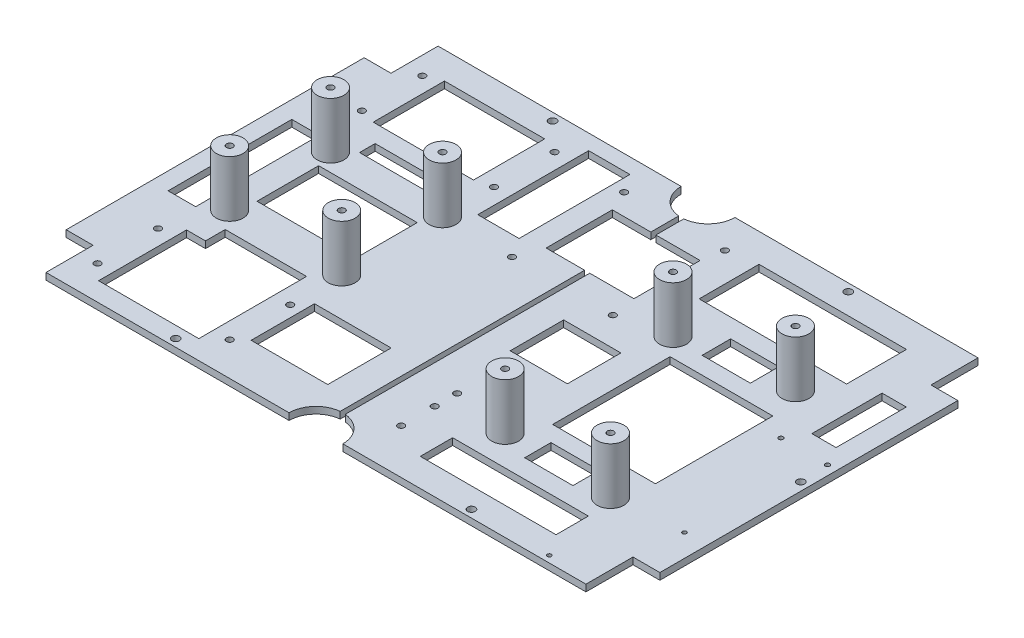
SolidWorks part; units mm, degrees
ref_plane "Płaszczyzna przednia" through (0, 0, 0) normal (0, 0, 1) x (1, 0, 0)
ref_plane "Płaszczyzna górna" through (0, 0, 0) normal (0, 1, 0) x (1, 0, 0)
ref_plane "Płaszczyzna prawa" through (0, 0, 0) normal (1, 0, 0) x (0, 0, -1)
sketch "Sketch1" plane through (0, 0, 0) normal (0, 1, 0) x (1, 0, 0)
  line L16 (-132.5, 87.5) -> (132.5, 87.5)
  line L18 (-132.5, 87.5) -> (-132.5, -87.5)
  line L19 (-132.5, -87.5) -> (132.5, -87.5)
  line L20 (132.5, 87.5) -> (132.5, -87.5)
  line L21 (-132.5, 87.5) -> (132.5, -87.5) construction
  line L22 (-132.5, -87.5) -> (132.5, 87.5) construction
  point P0 (0, 0)
  dimension "D2" = 175
  dimension "D1" = 265
extrude "Boss-Extrude3" add sketch "Sketch1" along normal blind 3
sketch "Sketch2" plane through (0, 3, 0) normal (0, 1, 0) x (1, 0, 0)
  line L2 (-53.5, -45.5) -> (-53.5, 45.5) construction
  line L10 (-132.5, -87.5) -> (-112.5, -87.5) construction
  line L11 (-132.5, -87.5) -> (-132.5, -72.5) construction
  line L12 (-132.5, -72.5) -> (-112.5, -72.5) construction
  line L13 (-112.5, -87.5) -> (-112.5, -72.5) construction
  line L14 (-112.5, -72.5) -> (-53.5, -72.5) construction
  line L15 (-112.5, -72.5) -> (-112.5, -45.5) construction
  line L16 (-112.5, -45.5) -> (-53.5, -45.5) construction
  line L17 (-53.5, -72.5) -> (-53.5, -45.5) construction
  line L18 (-53.5, 45.5) -> (-112.5, 45.5) construction
  line L19 (-53.5, 45.5) -> (-53.5, 72.5) construction
  line L20 (-53.5, 72.5) -> (-112.5, 72.5) construction
  line L21 (-112.5, 45.5) -> (-112.5, 72.5) construction
  line L22 (-53.5, -22.5) -> (-103.5, -22.5) construction
  line L23 (0, 87.5) -> (0, 72.5) construction
  line L28 (132.5, 87.5) -> (-132.5, 87.5) construction
  line L29 (0, 72.5) -> (22.5, 72.5) construction
  line L30 (22.5, 72.5) -> (22.5, 22.5) construction
  line L31 (22.5, 22.5) -> (-22.5, 22.5) construction
  line L32 (-22.5, 22.5) -> (-22.5, 72.5) construction
  line L33 (-22.5, 72.5) -> (0, 72.5) construction
  line L34 (0, -87.5) -> (0, -67.5) construction
  line L35 (-132.5, -87.5) -> (132.5, -87.5) construction
  line L36 (0, -67.5) -> (18, -67.5) construction
  line L37 (18, -67.5) -> (18, -52.5) construction
  line L38 (18, -52.5) -> (18, -42.5) construction
  line L39 (18, -42.5) -> (18, -27.5) construction
  line L40 (-53.5, -22.5) -> (-53.5, 22.5) construction
  line L45 (-53.5, 22.5) -> (-103.5, 22.5) construction
  line L46 (-103.5, -22.5) -> (-103.5, 22.5) construction
  circle A4 centre (18, -67.5) radius 1.45
  circle A5 centre (18, -52.5) radius 1.45
  circle A6 centre (18, -42.5) radius 1.45
  circle A7 centre (18, -27.5) radius 1.45
  circle A8 centre (-53.5, -72.5) radius 1.45
  circle A9 centre (-53.5, -45.5) radius 1.45
  circle A10 centre (-112.5, -45.5) radius 1.45
  circle A11 centre (-112.5, -72.5) radius 1.45
  circle A12 centre (-112.5, 45.5) radius 1.45
  circle A13 centre (-53.5, 45.5) radius 1.45
  circle A14 centre (-53.5, 72.5) radius 1.45
  circle A15 centre (-112.5, 72.5) radius 1.45
  circle A20 centre (-22.5, 22.5) radius 1.45
  circle A21 centre (22.5, 22.5) radius 1.45
  circle A22 centre (-22.5, 72.5) radius 1.45
  circle A23 centre (22.5, 72.5) radius 1.45
  dimension "D3" = 20
  dimension "D11" = 45
  dimension "D4" = 15
  dimension "D5" = 27
  dimension "D6" = 59
  dimension "D7" = 27
  dimension "D8" = 59
  dimension "D9" = 15
  dimension "D10" = 50
  dimension "D12" = 23
  dimension "D13" = 23
extrude "Cut-Extrude1" cut sketch "Sketch2" against normal blind 10
sketch "Sketch3" plane through (0, 3, 0) normal (0, 1, 0) x (1, 0, 0)
  line L0 (132.5, 0) -> (128.9, 0) construction
  line L1 (132.5, -87.5) -> (132.5, 87.5) construction
  line L2 (-132.5, 0) -> (-128.9, 0) construction
  line L3 (-132.5, 87.5) -> (-132.5, -87.5) construction
  line L4 (-128.9, 0) -> (-66, 0) construction
  line L5 (-66, 0) -> (-66, 84.1) construction
  line L6 (-66, 0) -> (-66, -84.1) construction
  line L7 (-66, 84.1) -> (66, 84.1) construction
  line L8 (-66, -84.1) -> (66, -84.1) construction
  circle A0 centre (-66, 84.1) radius 1.7
  circle A1 centre (-128.9, 0) radius 1.7
  circle A2 centre (-66, -84.1) radius 1.7
  circle A3 centre (66, -84.1) radius 1.7
  circle A4 centre (66, 84.1) radius 1.7
  circle A5 centre (128.9, 0) radius 1.7
extrude "Cut-Extrude2" cut sketch "Sketch3" against normal blind 10
sketch "Sketch4" plane through (0, 3, 0) normal (0, 1, 0) x (1, 0, 0)
  line L0 (132.5, 87.5) -> (-132.5, 87.5) construction
  line L1 (-132.5, -87.5) -> (132.5, -87.5) construction
  line L3 (-132.5, 87.5) -> (-120.5, 87.5)
  line L4 (-132.5, 87.5) -> (-132.5, 66.5)
  line L5 (-132.5, 66.5) -> (-120.5, 66.5)
  line L6 (-120.5, 87.5) -> (-120.5, 66.5)
  line L7 (-132.5, -87.5) -> (-120.5, -87.5)
  line L8 (-132.5, -87.5) -> (-132.5, -66.5)
  line L9 (-132.5, -66.5) -> (-120.5, -66.5)
  line L10 (-120.5, -87.5) -> (-120.5, -66.5)
  line L11 (132.5, -87.5) -> (120.5, -87.5)
  line L12 (132.5, -87.5) -> (132.5, -66.5)
  line L13 (132.5, -66.5) -> (120.5, -66.5)
  line L14 (120.5, -87.5) -> (120.5, -66.5)
  line L15 (132.5, 87.5) -> (120.5, 87.5)
  line L16 (132.5, 87.5) -> (132.5, 66.5)
  line L17 (132.5, 66.5) -> (120.5, 66.5)
  line L18 (120.5, 87.5) -> (120.5, 66.5)
  circle A0 centre (0, 87.5) radius 12
  circle A1 centre (0, -87.5) radius 12
  dimension "D1" = 21
  dimension "D2" = 12
  dimension "D3" = 21
  dimension "D4" = 12
  dimension "D5" = 12
  dimension "D6" = 21
  dimension "D7" = 12
  dimension "D8" = 21
extrude "Cut-Extrude3" cut sketch "Sketch4" against normal blind 10
sketch "Sketch5" plane through (0, 3, 0) normal (0, 1, 0) x (1, 0, 0)
  circle A0 centre (-53.5, 22.5) radius 6
  circle A1 centre (-53.5, -22.5) radius 6
  circle A2 centre (-103.5, -22.5) radius 6
  circle A3 centre (-103.5, 22.5) radius 6
  dimension "D1" = 45
  dimension "D2" = 50
  dimension "D3" = 50
  dimension "D4" = 45
extrude "Boss-Extrude4" add sketch "Sketch5" along normal blind 25
sketch "Sketch6" plane through (0, 28, 0) normal (0, 1, 0) x (1, 0, 0)
  circle A0 centre (-103.5, 22.5) radius 1.45
  circle A1 centre (-53.5, 22.5) radius 1.45
  circle A2 centre (-53.5, -22.5) radius 1.45
  circle A3 centre (-103.5, -22.5) radius 1.45
extrude "Cut-Extrude4" cut sketch "Sketch6" against normal blind 16
sketch "Sketch7" plane through (0, 3, 0) normal (0, 1, 0) x (1, 0, 0)
  line L1 (-1.1414, -75.5544) -> (1.1414, -75.5544)
  line L2 (-1.1414, -75.5544) -> (-1.1414, 75.5544)
  line L3 (-1.1414, 75.5544) -> (1.1414, 75.5544)
  line L4 (1.1414, -75.5544) -> (1.1414, 75.5544)
  line L5 (-1.1414, -75.5544) -> (1.1414, 75.5544) construction
  line L6 (-1.1414, 75.5544) -> (1.1414, -75.5544) construction
  arc A0 (-12, 87.5) -> (12, 87.5) centre (0, 87.5) ccw construction
  point P0 (0, 0)
extrude "Cut-Extrude5" cut sketch "Sketch7" against normal blind 16
sketch "Sketch8" plane through (0, 3, 0) normal (0, 1, 0) x (1, 0, 0)
  line L1 (-100.9203, -12.8956) -> (-56.9163, -12.8956)
  line L2 (-100.9203, -12.8956) -> (-100.9203, 14.6069)
  line L3 (-100.9203, 14.6069) -> (-56.9163, 14.6069)
  line L4 (-56.9163, -12.8956) -> (-56.9163, 14.6069)
  line L5 (-112.5004, -28.6939) -> (-124.8041, -28.6939)
  line L6 (-112.5004, -28.6939) -> (-112.5004, 26.5182)
  line L7 (-112.5004, 26.5182) -> (-124.8041, 26.5182)
  line L8 (-124.8041, -28.6939) -> (-124.8041, 26.5182)
  line L9 (-105.568, 43.6252) -> (-60.8155, 43.6252)
  line L10 (-105.568, 43.6252) -> (-105.568, 75.4196)
  line L11 (-105.568, 75.4196) -> (-60.8155, 75.4196)
  line L12 (-60.8155, 43.6252) -> (-60.8155, 75.4196)
  line L21 (-46.4644, 80.6781) -> (-28.0466, 80.6781)
  line L22 (-46.4644, 80.6781) -> (-46.4644, 31.1977)
  line L23 (-46.4644, 31.1977) -> (-28.0466, 31.1977)
  line L24 (-28.0466, 80.6781) -> (-28.0466, 31.1977)
  line L25 (-96.8686, 28.8192) -> (-61.2463, 28.8192)
  line L26 (-96.8686, 28.8192) -> (-96.8686, 35.7775)
  line L27 (-96.8686, 35.7775) -> (-61.2463, 35.7775)
  line L28 (-61.2463, 28.8192) -> (-61.2463, 35.7775)
  line L29 (-105.568, -78.974) -> (-60.8155, -78.974)
  line L30 (-105.568, -78.974) -> (-105.568, -39.7113)
  line L31 (-105.568, -39.7113) -> (-60.8155, -39.7113)
  line L32 (-60.8155, -78.974) -> (-60.8155, -39.7113)
  line L33 (-60.8155, -39.7113) -> (-97.1012, -39.7113)
  line L34 (-60.8155, -39.7113) -> (-60.8155, -30.8994)
  line L35 (-60.8155, -30.8994) -> (-97.1012, -30.8994)
  line L36 (-97.1012, -39.7113) -> (-97.1012, -30.8994)
  line L37 (-48.4867, -67.9542) -> (-14.283, -67.9542)
  line L38 (-48.4867, -67.9542) -> (-48.4867, -39.6743)
  line L39 (-48.4867, -39.6743) -> (-14.283, -39.6743)
  line L40 (-14.283, -67.9542) -> (-14.283, -39.6743)
  line L42 (-18.3295, 33.5586) -> (20.8655, 33.5586)
  line L43 (-18.3295, 33.5586) -> (-18.3295, 63.0967)
  line L44 (-18.3295, 63.0967) -> (20.8655, 63.0967)
  line L45 (20.8655, 33.5586) -> (20.8655, 63.0967)
extrude "Cut-Extrude6" cut sketch "Sketch8" against normal blind 10
sketch "Sketch9" plane through (0, 3, 0) normal (0, 1, 0) x (1, 0, 0)
  line L0 (132.5, -33.0356) -> (92.5, -33.0356) construction
  line L1 (132.5, -66.5) -> (132.5, 66.5) construction
  line L2 (92.5, -87.5) -> (92.5, -62.5) construction
  line L3 (12, -87.5) -> (120.5, -87.5) construction
  line L4 (92.5, -62.5) -> (92.5, -48.53) construction
  line L5 (44.2, -47.26) -> (44.2, -87.5) construction
  line L6 (92.5, -48.53) -> (92.5, 34.02) construction
  line L7 (44.2, -47.26) -> (44.2, 27.67) construction
  circle A0 centre (92.5, -48.53) radius 6
  circle A1 centre (44.2, -47.26) radius 6
  circle A2 centre (92.5, 34.02) radius 6
  circle A3 centre (44.2, 27.67) radius 6
  dimension "D5" = 82.55
  dimension "D6" = 74.93
  dimension "D1" = 40
  dimension "D2" = 25
  dimension "D3" = 13.97
  dimension "D4" = 40.24
extrude "Boss-Extrude5" add sketch "Sketch9" along normal blind 25
sketch "Sketch10" plane through (0, 28, 0) normal (0, 1, 0) x (1, 0, 0)
  circle A0 centre (44.2, 27.67) radius 1.45
  circle A1 centre (92.5, 34.02) radius 1.45
  circle A2 centre (44.2, -47.26) radius 1.45
  circle A3 centre (92.5, -48.53) radius 1.45
extrude "Cut-Extrude7" cut sketch "Sketch10" against normal blind 15
sketch "Sketch11" plane through (0, 3, 0) normal (0, 1, 0) x (1, 0, 0)
  line L0 (92.5, -48.53) -> (122.5, -48.53) construction
  line L1 (122.5, -48.53) -> (122.5, -45.53) construction
  line L2 (122.5, -45.53) -> (122.5, -84.53) construction
  line L3 (122.5, -84.53) -> (101.2, -84.53) construction
  line L4 (92.5, 34.02) -> (92.5, 12.52) construction
  line L5 (92.5, 12.52) -> (107.5, 12.52) construction
  line L6 (107.5, 12.52) -> (128.3, 12.52) construction
  circle A1 centre (122.5, -45.53) radius 0.9
  circle A2 centre (101.2, -84.53) radius 0.9
  circle A3 centre (107.5, 12.52) radius 1
  circle A4 centre (128.3, 12.52) radius 1
  dimension "D3" = 39
  dimension "D5" = 21.5
  dimension "D7" = 20.8
  dimension "D1" = 30
  dimension "D2" = 3
  dimension "D4" = 21.3
  dimension "D6" = 15
extrude "Cut-Extrude8" cut sketch "Sketch11" against normal blind 20
sketch "Sketch12" plane through (0, 3, 0) normal (0, 1, 0) x (1, 0, 0)
  line L1 (35.4781, 74.7773) -> (101.3027, 74.7773)
  line L2 (35.4781, 74.7773) -> (35.4781, 48.0358)
  line L3 (35.4781, 48.0358) -> (101.3027, 48.0358)
  line L4 (101.3027, 74.7773) -> (101.3027, 48.0358)
  line L5 (51.337, -33.1748) -> (97.2099, -33.1748)
  line L6 (51.337, -33.1748) -> (51.337, 19.2193)
  line L7 (51.337, 19.2193) -> (97.2099, 19.2193)
  line L8 (97.2099, -33.1748) -> (97.2099, 19.2193)
  line L9 (13.3712, -14.1986) -> (38.9219, -14.1986)
  line L10 (13.3712, -14.1986) -> (13.3712, 9.6857)
  line L11 (13.3712, 9.6857) -> (38.9219, 9.6857)
  line L12 (38.9219, -14.1986) -> (38.9219, 9.6857)
  line L13 (34.1314, -75.0602) -> (94.7145, -75.0602)
  line L14 (34.1314, -75.0602) -> (34.1314, -60.6357)
  line L15 (34.1314, -60.6357) -> (94.7145, -60.6357)
  line L16 (94.7145, -75.0602) -> (94.7145, -60.6357)
  line L17 (112.7311, 21.1201) -> (123.5283, 21.1201)
  line L18 (112.7311, 21.1201) -> (112.7311, 52.4592)
  line L19 (112.7311, 52.4592) -> (123.5283, 52.4592)
  line L20 (123.5283, 21.1201) -> (123.5283, 52.4592)
  line L21 (57.9675, 26.8924) -> (79.4985, 26.8924)
  line L22 (57.9675, 26.8924) -> (57.9675, 39.6197)
  line L23 (57.9675, 39.6197) -> (79.4985, 39.6197)
  line L24 (79.4985, 26.8924) -> (79.4985, 39.6197)
  line L25 (57.9675, -52.3018) -> (79.4985, -52.3018)
  line L26 (57.9675, -52.3018) -> (57.9675, -40.5662)
  line L27 (57.9675, -40.5662) -> (79.4985, -40.5662)
  line L28 (79.4985, -52.3018) -> (79.4985, -40.5662)
extrude "Cut-Extrude9" cut sketch "Sketch12" against normal blind 20
